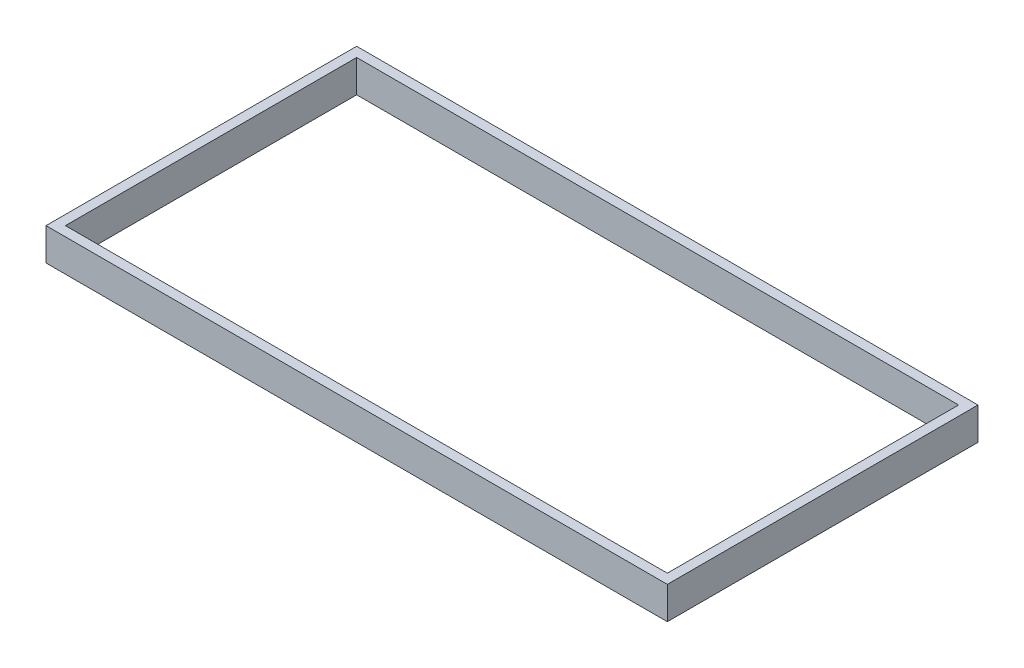
SolidWorks part; units mm, degrees
material "Cedar"
ref_plane "Front Plane" through (0, 0, 0) normal (0, 0, 1) x (1, 0, 0)
ref_plane "Top Plane" through (0, 0, 0) normal (0, 1, 0) x (1, 0, 0)
ref_plane "Right Plane" through (0, 0, 0) normal (1, 0, 0) x (0, 0, -1)
sketch "Sketch1" plane through (0, 0, 0) normal (0, 1, 0) x (1, 0, 0)
  line L0 (0, 285.75) -> (0, 304.8) construction
  line L1 (-590.55, -285.75) -> (590.55, -285.75)
  line L2 (-590.55, -285.75) -> (-590.55, 285.75)
  line L3 (-590.55, 285.75) -> (590.55, 285.75)
  line L4 (590.55, -285.75) -> (590.55, 285.75)
  line L5 (-590.55, -285.75) -> (590.55, 285.75) construction
  line L6 (-590.55, 285.75) -> (590.55, -285.75) construction
  line L7 (-609.6, -304.8) -> (609.6, -304.8)
  line L8 (-609.6, -304.8) -> (-609.6, 304.8)
  line L9 (-609.6, 304.8) -> (609.6, 304.8)
  line L10 (609.6, -304.8) -> (609.6, 304.8)
  line L11 (-609.6, -304.8) -> (609.6, 304.8) construction
  line L12 (-609.6, 304.8) -> (609.6, -304.8) construction
  line L13 (-590.55, 0) -> (-609.6, 0) construction
  point P0 (0, 0)
  point P6 (0, 0)
  dimension "D1" = 19.05
  dimension "D2" = 1219.2
  dimension "D3" = 609.6
extrude "Boss-Extrude1" add sketch "Sketch1" along normal blind 63.5
